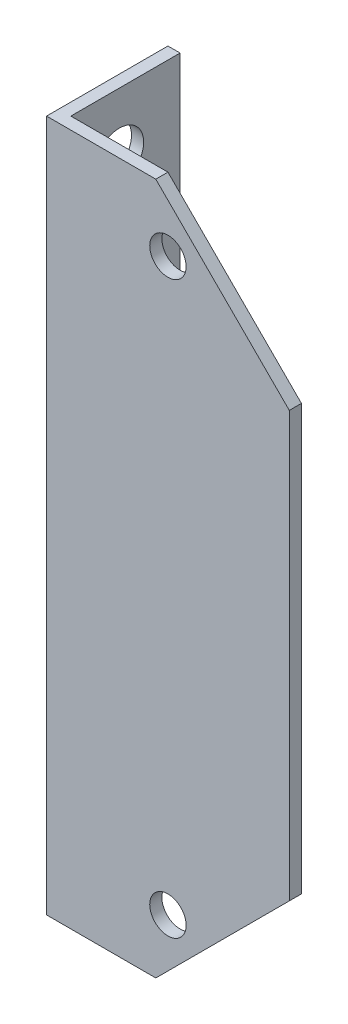
SolidWorks part; units mm, degrees
ref_plane "Plan de face" through (0, 0, 0) normal (0, 0, 1) x (1, 0, 0)
ref_plane "Plan de dessus" through (0, 0, 0) normal (0, 1, 0) x (1, 0, 0)
ref_plane "Plan de droite" through (0, 0, 0) normal (1, 0, 0) x (0, 0, -1)
sketch "Esquisse1" plane through (0, 0, 0) normal (0, 1, 0) x (1, 0, 0)
  line L0 (-11, 8.5) -> (-11, -1.5)
  line L1 (-11, -1.5) -> (9, -1.5)
  line L2 (9, -1.5) -> (9, -0.5)
  line L3 (9, -0.5) -> (-10, -0.5)
  line L4 (-10, -0.5) -> (-10, 8.5)
  line L5 (-10, 8.5) -> (-11, 8.5)
  dimension "D1" = 1
  dimension "D2" = 1
  dimension "D3" = 0.5
  dimension "D4" = 10
  dimension "D5" = 10
  dimension "D6" = 20
extrude "Boss.-Extru.1" add sketch "Esquisse1" along normal blind 57
sketch "Esquisse2" plane through (-11, 0, 0) normal (-1, 0, 0) x (0, 0, 1)
  line L0 (1.5, 57) -> (1.5, 0) construction
  line L1 (-8.5, 0) -> (1.5, 0) construction
  circle A0 centre (-3.5, 52.14) radius 2
  circle A1 centre (-3.5, 5) radius 2
  dimension "D1" = 4
  dimension "D2" = 4
  dimension "D3" = 5
  dimension "D4" = 5
  dimension "D5" = 47.14
  dimension "D6" = 5
extrude "Enlèv. mat.-Extru.1" cut sketch "Esquisse2" against normal blind 50
sketch "Esquisse3" plane through (0, 0, 0.5) normal (0, 0, -1) x (-1, 0, 0)
  line L0 (-9, 0) -> (10, 0) construction
  line L1 (-9, 57) -> (-9, 0) construction
  line L2 (2, 57) -> (-9, 46)
  line L3 (-9, 57) -> (10, 57) construction
  line L4 (-9, 57) -> (-9, 46)
  line L5 (-9, 57) -> (2, 57)
  line L6 (-9, 0) -> (-9, 11)
  line L7 (-9, 11) -> (2, 0)
  line L8 (2, 0) -> (-9, 0)
  circle A0 centre (1, 52) radius 1.5
  circle A1 centre (1, 5) radius 1.5
  dimension "D1" = 5
  dimension "D5" = 3
  dimension "D6" = 3
  dimension "D2" = 10
  dimension "D3" = 10
  dimension "D4" = 47
  dimension "D7" = 11
  dimension "D8" = 11
  dimension "D9" = 11
  dimension "D10" = 11
extrude "Enlèv. mat.-Extru.2" cut sketch "Esquisse3" against normal blind 50
